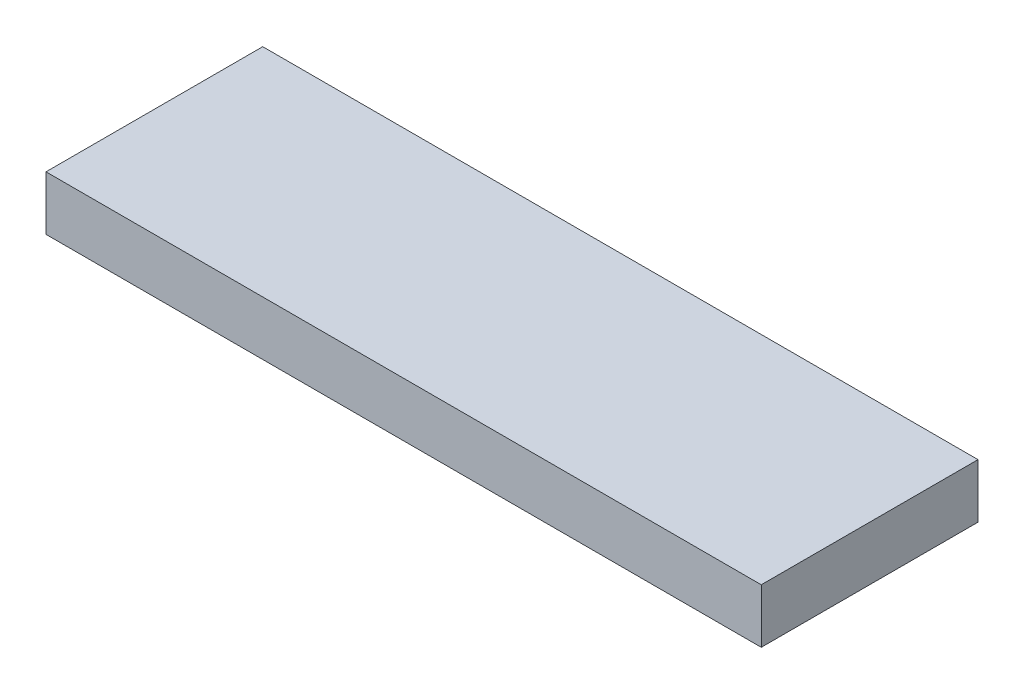
SolidWorks part; units mm, degrees
ref_plane "Front Plane" through (0, 0, 0) normal (0, 0, 1) x (1, 0, 0)
ref_plane "Top Plane" through (0, 0, 0) normal (0, 1, 0) x (1, 0, 0)
ref_plane "Right Plane" through (0, 0, 0) normal (1, 0, 0) x (0, 0, -1)
sketch "Sketch1" plane through (0, 0, 0) normal (0, 1, 0) x (1, 0, 0)
  line L1 (-20.955, 6.35) -> (20.955, 6.35)
  line L2 (-20.955, 6.35) -> (-20.955, -6.35)
  line L3 (-20.955, -6.35) -> (20.955, -6.35)
  line L4 (20.955, 6.35) -> (20.955, -6.35)
  point P4 (0, 6.35)
  point P5 (20.955, 0)
  dimension "D1" = 41.91
  dimension "D2" = 12.7
extrude "Boss-Extrude1" add sketch "Sketch1" along normal blind 3.175
